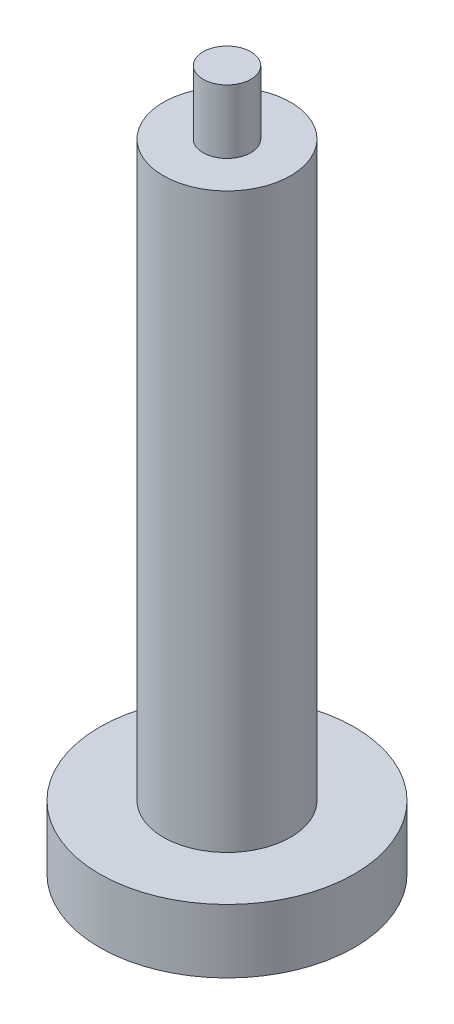
SolidWorks part; units mm, degrees
ref_plane "Front Plane" through (0, 0, 0) normal (0, 0, 1) x (1, 0, 0)
ref_plane "Top Plane" through (0, 0, 0) normal (0, 1, 0) x (1, 0, 0)
ref_plane "Right Plane" through (0, 0, 0) normal (1, 0, 0) x (0, 0, -1)
sketch "Sketch1" plane through (0, 0, 0) normal (0, 1, 0) x (1, 0, 0)
  circle A0 centre (0, 0) radius 25.4
extrude "Boss-Extrude1" add sketch "Sketch1" along normal mid plane 127
sketch "Sketch2" plane through (0, 63.5, 0) normal (0, 1, 0) x (1, 0, 0)
  circle A0 centre (0, 0) radius 25.4
  circle A1 centre (0, 0) radius 12.7
extrude "Cut-Extrude1" cut sketch "Sketch2" against normal blind 114.3
sketch "Sketch3" plane through (0, 63.5, 0) normal (0, 1, 0) x (1, 0, 0)
  circle A0 centre (0, 0) radius 4.7625
extrude "Boss-Extrude2" add sketch "Sketch3" along normal blind 12.7
sketch "Sketch4" plane through (0, -63.5, 0) normal (0, -1, 0) x (1, 0, 0)
  circle A0 centre (0, 0) radius 19.05
extrude "Cut-Extrude2" cut sketch "Sketch4" against normal blind 2.54
hole_wizard "3/8-16 Tapped Hole1" positions "Sketch6" profile "Sketch5" tap size "3/8-16" standard "ANSI Inch"
sketch "Sketch6" plane through (0, -60.96, 0) normal (0, -1, 0) x (-1, 0, 0)
  point P0 (0, 0)
sketch "Sketch5" plane through (0, -60.96, 0) normal (1, 0, 0) x (0, 0, -1)
  line L0 (0, 0) -> (0, 29.3087)
  line L1 (0, 29.3087) -> (3.9687, 26.924)
  line L2 (3.9687, 26.924) -> (3.9687, 0)
  line L5 (3.9687, 0) -> (0, 0)
  line L10 (0, 29.3087) -> (-3.9688, 26.924) construction
  line L11 (0, -6.35) -> (0, 107.95) construction
  dimension "Tap Drill Dia." = 7.9375
  dimension "Tap Drill Depth" = 26.924
  dimension "Drill Angle" = 118
cosmetic thread "Hole Thread1" parameters "D1"=19.05, "D2"=9.525
